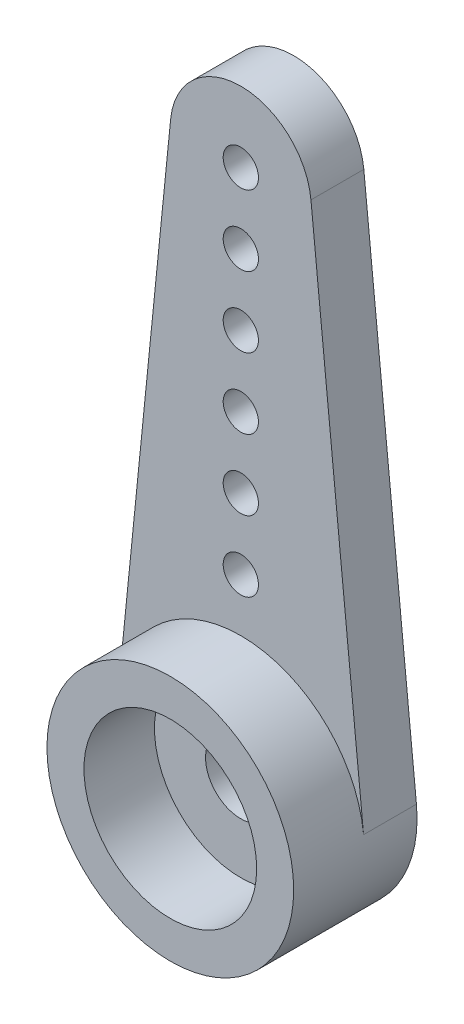
SolidWorks part; units mm, degrees
ref_plane "Plan de face" through (0, 0, 0) normal (0, 0, 1) x (1, 0, 0)
ref_plane "Plan de dessus" through (0, 0, 0) normal (0, 1, 0) x (1, 0, 0)
ref_plane "Plan de droite" through (0, 0, 0) normal (1, 0, 0) x (0, 0, -1)
sketch "Esquisse1" plane through (0, 0, 0) normal (0, 0, 1) x (1, 0, 0)
  line L0 (-1.99, 15.2) -> (-3.4825, 0.35)
  line L1 (1.99, 15.2) -> (3.4825, 0.35)
  arc A0 (-3.4825, 0.35) -> (3.4825, 0.35) centre (0, 0) ccw
  arc A1 (1.99, 15.2) -> (-1.99, 15.2) centre (0, 15) ccw
  circle A2 centre (0, 0) radius 1
  circle A3 centre (0, 15) radius 0.5
  circle A4 centre (0, 13) radius 0.5
  circle A5 centre (0, 11) radius 0.5
  circle A6 centre (0, 9) radius 0.5
  circle A7 centre (0, 7) radius 0.5
  circle A8 centre (0, 5) radius 0.5
  dimension "D1" = 4
  dimension "D2" = 7
  dimension "D4" = 2
  dimension "D5" = 1
  dimension "D3" = 15
  dimension "D6" = 6
extrude "Boss.-Extru.1" add sketch "Esquisse1" along normal blind 1.5
sketch "Esquisse3" plane through (0, 0, 1.5) normal (0, 0, 1) x (1, 0, 0)
  circle A0 centre (0, 0) radius 3.5
  circle A1 centre (0, 0) radius 1
  arc A2 (-3.4825, 0.35) -> (3.4825, 0.35) centre (0, 0) ccw construction
  circle A3 centre (0, 0) radius 1 construction
extrude "Boss.-Extru.2" add sketch "Esquisse3" along normal blind 2
sketch "Esquisse4" plane through (0, 0, 3.5) normal (0, 0, 1) x (1, 0, 0)
  circle A0 centre (0, 0) radius 2.45
  dimension "D1" = 4.9
extrude "Enlèv. mat.-Extru.1" cut sketch "Esquisse4" against normal blind 2
